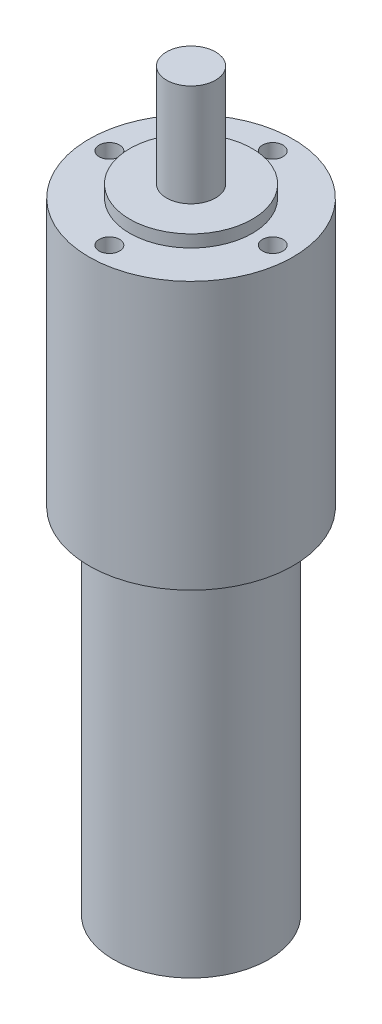
SolidWorks part; units mm, degrees
ref_plane "Front Plane" through (0, 0, 0) normal (0, 0, 1) x (1, 0, 0)
ref_plane "Top Plane" through (0, 0, 0) normal (0, 1, 0) x (1, 0, 0)
ref_plane "Right Plane" through (0, 0, 0) normal (1, 0, 0) x (0, 0, -1)
sketch "Sketch1" plane through (0, 0, 0) normal (0, 1, 0) x (1, 0, 0)
  circle A0 centre (0, 0) radius 25
  dimension "D1" = 50
extrude "Boss-Extrude1" add sketch "Sketch1" along normal blind 65.5
sketch "Sketch2" plane through (0, 65.5, 0) normal (0, 1, 0) x (1, 0, 0)
  circle A0 centre (0, 0) radius 15
  dimension "D1" = 30
extrude "Boss-Extrude2" add sketch "Sketch2" along normal blind 3
sketch "Sketch3" plane through (0, 68.5, 0) normal (0, 1, 0) x (1, 0, 0)
  circle A0 centre (0, 0) radius 6
  dimension "D1" = 12
extrude "Boss-Extrude3" add sketch "Sketch3" along normal blind 25
sketch "Sketch4" plane through (0, 0, 0) normal (0, -1, 0) x (1, 0, 0)
  circle A0 centre (0, 0) radius 19
  dimension "D1" = 38
extrude "Boss-Extrude4" add sketch "Sketch4" along normal blind 86.5
sketch "Sketch5" plane through (0, 65.5, 0) normal (0, 1, 0) x (1, 0, 0)
  circle A0 centre (0, 0) radius 20 construction
  circle A1 centre (0, 20) radius 2.5
  circle A2 centre (20, 0) radius 2.5
  circle A3 centre (0, -20) radius 2.5
  circle A4 centre (-20, 0) radius 2.5
  point P14 (0, 0)
  dimension "D1" = 40
  dimension "D2" = 5
  dimension "D3" = 4
extrude "Cut-Extrude1" cut sketch "Sketch5" against normal blind 10
